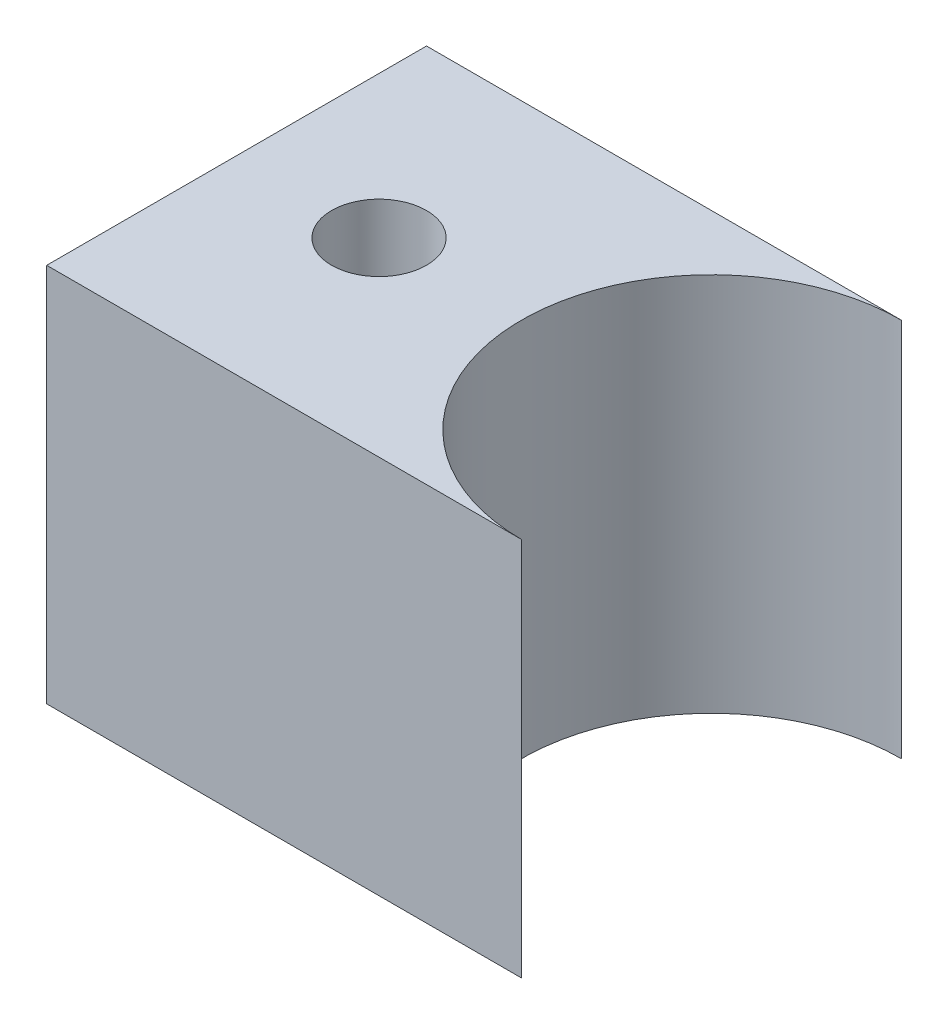
SolidWorks part; units mm, degrees
material "Cast Carbon Steel"
ref_plane "Front Plane" through (0, 0, 0) normal (0, 0, 1) x (1, 0, 0)
ref_plane "Top Plane" through (0, 0, 0) normal (0, 1, 0) x (1, 0, 0)
ref_plane "Right Plane" through (0, 0, 0) normal (1, 0, 0) x (0, 0, -1)
sketch "Sketch2" plane through (0, 0, 0) normal (0, 1, 0) x (1, 0, 0)
  line L1 (-15.875, -12.7) -> (15.875, -12.7)
  line L2 (-15.875, -12.7) -> (-15.875, 12.7)
  line L3 (-15.875, 12.7) -> (15.875, 12.7)
  line L4 (15.875, -12.7) -> (15.875, 12.7)
  line L5 (-15.875, -12.7) -> (15.875, 12.7) construction
  line L6 (-15.875, 12.7) -> (15.875, -12.7) construction
  circle A1 centre (15.875, 0) radius 12.7
  circle A2 centre (-6.35, 0) radius 3.175
  point P0 (0, 0)
  dimension "D3" = 6.35
  dimension "D1" = 31.75
  dimension "D2" = 25.4
  dimension "D4" = 9.525
  dimension "D5" = 12.7
extrude "Boss-Extrude2" add sketch "Sketch2" along normal blind 25.4 contours A1 L3 L2 L1 A2
sketch "Sketch3" plane through (-15.875, 0, 0) normal (-1, 0, 0) x (0, 0, 1)
  line L0 (12.7, 25.4) -> (-12.7, 25.4) construction
  circle A0 centre (0, 12.7) radius 4.7625
  dimension "D1" = 9.525
  dimension "D2" = 12.7
  dimension "D3" = 12.7
extrude "Cut-Extrude1" cut sketch "Sketch3" against normal blind 14.2875
